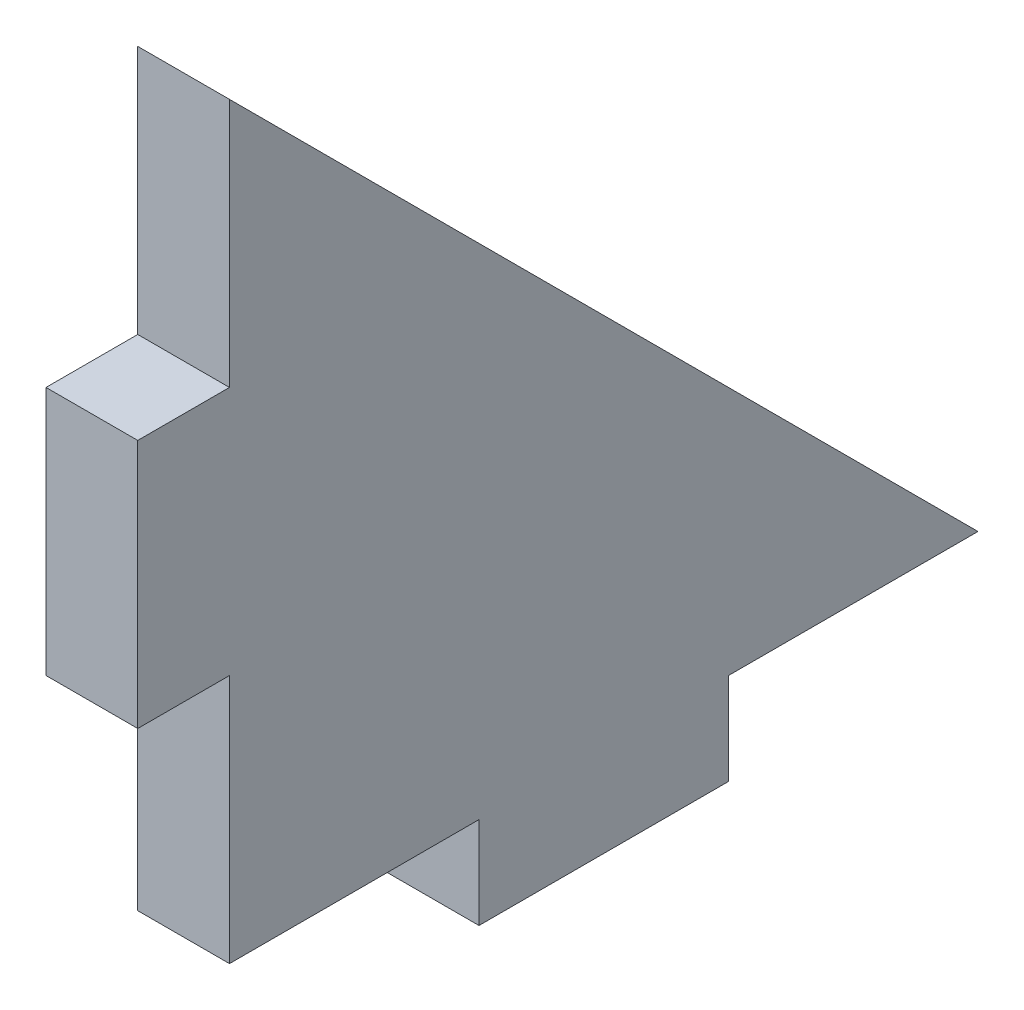
SolidWorks part; units mm, degrees
ref_plane "Front Plane" through (0, 0, 0) normal (0, 0, 1) x (1, 0, 0)
ref_plane "Top Plane" through (0, 0, 0) normal (0, 1, 0) x (1, 0, 0)
ref_plane "Right Plane" through (0, 0, 0) normal (1, 0, 0) x (0, 0, -1)
sketch "Sketch1" plane through (0, 0, 0) normal (1, 0, 0) x (0, 0, -1)
  line L0 (0, 21.2132) -> (21.2132, 0)
  line L1 (0, 0) -> (7.0711, 0)
  line L2 (0, 0) -> (0, 7.0711)
  line L3 (0, 14.1421) -> (0, 21.2132)
  line L4 (0, 14.1421) -> (-2.6, 14.1421)
  line L5 (14.1421, 0) -> (21.2132, 0)
  line L6 (0, 7.0711) -> (-2.6, 7.0711)
  line L7 (-2.6, 14.1421) -> (-2.6, 7.0711)
  line L9 (7.0711, 0) -> (7.0711, -2.6)
  line L10 (7.0711, -2.6) -> (14.1421, -2.6)
  line L11 (14.1421, 0) -> (14.1421, -2.6)
  dimension "D1" = 2.6
  dimension "D2" = 30
extrude "Boss-Extrude1" add sketch "Sketch1" along normal blind 2.6
equation "\"mdf\"=\"mdf@fmv1.assembly\""
equation "\"D1@Sketch1\"=\"mdf\""
equation "\"D1@Boss-Extrude1\"=\"mdf\""
